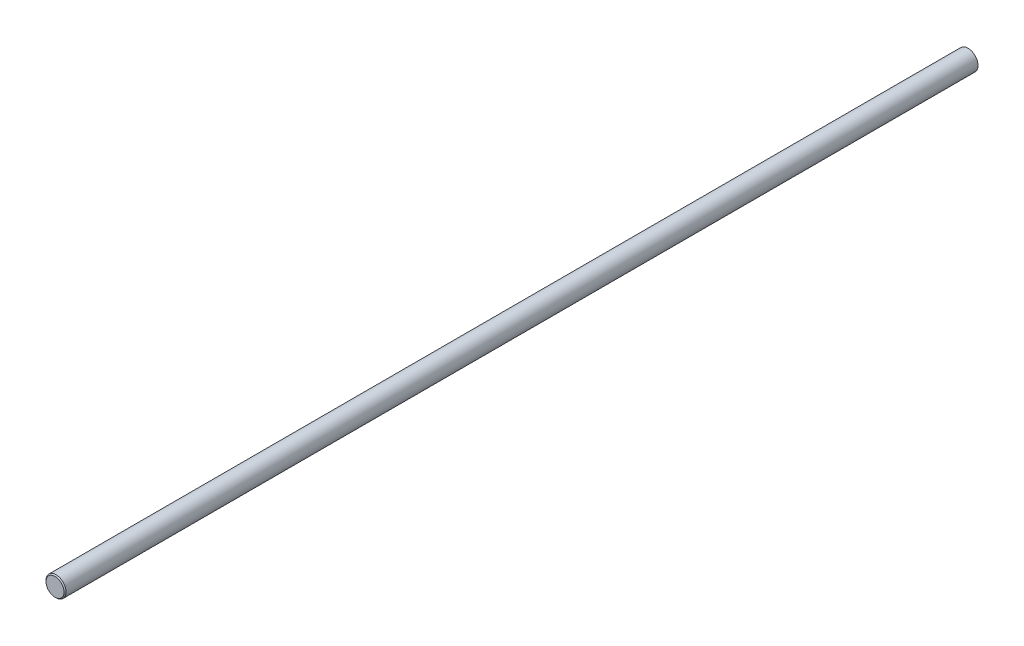
SolidWorks part; units mm, degrees
ref_plane "Plano frontal" through (0, 0, 0) normal (0, 0, 1) x (1, 0, 0)
ref_plane "Plano superior" through (0, 0, 0) normal (0, 1, 0) x (1, 0, 0)
ref_plane "Plano direito" through (0, 0, 0) normal (1, 0, 0) x (0, 0, -1)
sketch "Esboço1" plane through (0, 0, 0) normal (0, 1, 0) x (1, 0, 0)
  line L0 (15.48, -1501.5875) -> (0, -1501.5875)
  line L1 (0, -1501.5875) -> (0, -1525.5)
  line L2 (0, -1525.5) -> (15.075, -1525.5)
  line L3 (15.075, -1525.5) -> (16.75, -1523.825)
  line L4 (16.75, -1523.825) -> (16.75, 0)
  line L5 (16.75, 0) -> (15.48, 0)
  line L6 (15.48, 0) -> (15.48, -1501.5875)
  line L7 (0, 0) -> (0, -1525.5) construction
  dimension "D1" = 30.96
  dimension "D2" = 33.5
  dimension "D3" = 1501.5875
  dimension "D4" = 23.9125
  dimension "D5" = 1.675
  dimension "D6" = 45
revolve "Revolução1" add sketch "Esboço1" angle 360 about L7
